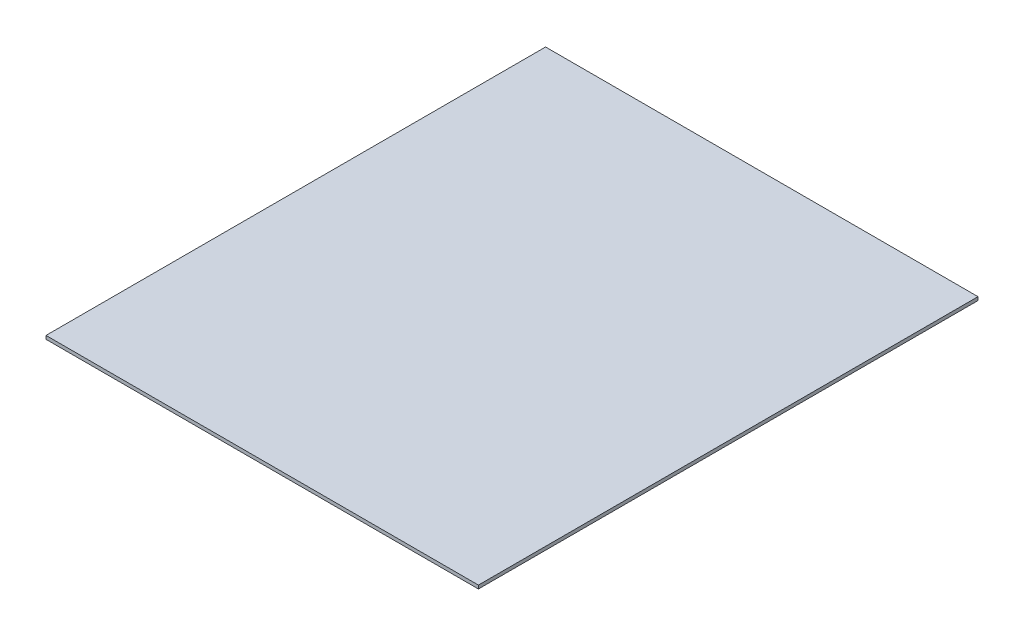
SolidWorks part; units mm, degrees
material "PPE"
ref_plane "Front Plane" through (0, 0, 0) normal (0, 0, 1) x (1, 0, 0)
ref_plane "Top Plane" through (0, 0, 0) normal (0, 1, 0) x (1, 0, 0)
ref_plane "Right Plane" through (0, 0, 0) normal (1, 0, 0) x (0, 0, -1)
sketch "Sketch1" plane through (0, 0, 0) normal (0, 1, 0) x (1, 0, 0)
  line L1 (-190, -219.5) -> (190, -219.5)
  line L2 (-190, -219.5) -> (-190, 219.5)
  line L3 (-190, 219.5) -> (190, 219.5)
  line L4 (190, -219.5) -> (190, 219.5)
  line L5 (-190, -219.5) -> (190, 219.5) construction
  line L6 (-190, 219.5) -> (190, -219.5) construction
  point P0 (0, 0)
  dimension "D1" = 380
  dimension "D2" = 439
extrude "Boss-Extrude1" add sketch "Sketch1" along normal blind 3
